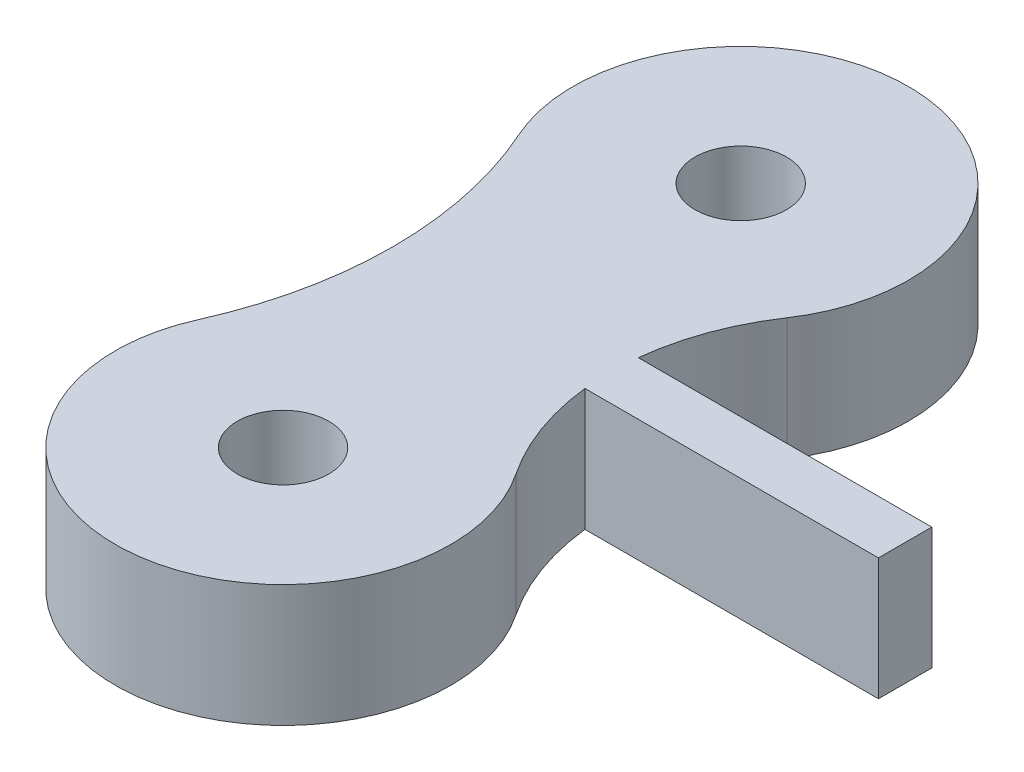
SolidWorks part; units mm, degrees
ref_plane "Front Plane" through (0, 0, 0) normal (0, 0, 1) x (1, 0, 0)
ref_plane "Top Plane" through (0, 0, 0) normal (0, 1, 0) x (1, 0, 0)
ref_plane "Right Plane" through (0, 0, 0) normal (1, 0, 0) x (0, 0, -1)
sketch "Sketch1" plane through (0, 0, 0) normal (0, 1, 0) x (1, 0, 0)
  line L0 (3.269, -6.6256) -> (12.8867, -6.6256)
  line L1 (12.8867, -6.6256) -> (12.8867, -8.3744)
  line L2 (12.8867, -8.3744) -> (3.269, -8.3744)
  circle A0 centre (0, 0) radius 1.5
  circle A1 centre (0, -15) radius 1.5
  arc A2 (-5.0211, -12.7554) -> (4.5701, -11.94) centre (0, -15) ccw
  arc A3 (4.5701, -3.06) -> (-5.0211, -2.2446) centre (0, 0) ccw
  arc A4 (-5.0211, -2.2446) -> (-5.0211, -12.7554) centre (-16.7777, -7.5) cw
  arc A5 (4.5701, -3.06) -> (3.269, -6.6256) centre (11.2011, -7.5) ccw
  arc A6 (3.269, -8.3744) -> (4.5701, -11.94) centre (11.2011, -7.5) ccw
  dimension "D1" = 3
  dimension "D2" = 4
  dimension "D3" = 15
extrude "Boss-Extrude1" add sketch "Sketch1" along normal blind 4
